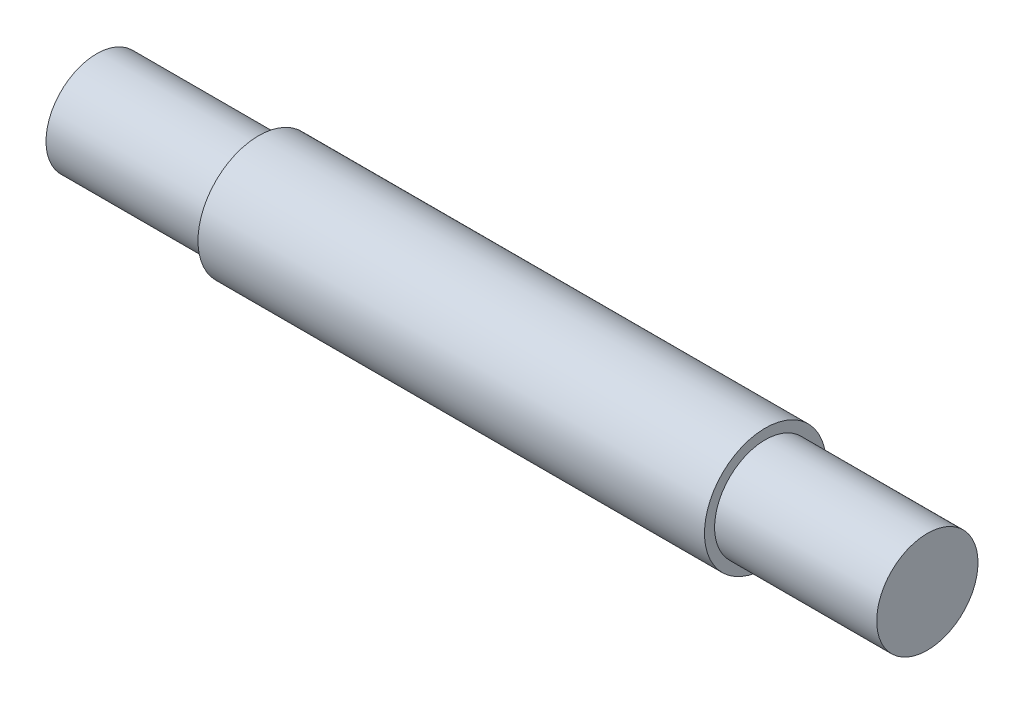
SolidWorks part; units mm, degrees
ref_plane "Ön Düzlem" through (0, 0, 0) normal (0, 0, 1) x (1, 0, 0)
ref_plane "Üst Düzlem" through (0, 0, 0) normal (0, 1, 0) x (1, 0, 0)
ref_plane "Sağ Düzlem" through (0, 0, 0) normal (1, 0, 0) x (0, 0, -1)
sketch "Çizim1" plane through (0, 0, 0) normal (1, 0, 0) x (0, 0, -1)
  circle A0 centre (0, 0) radius 6
extrude "Yükseklik-Ekstrüzyon1" add sketch "Çizim1" along normal blind 50
sketch "Çizim2" plane through (0, 0, 0) normal (-1, 0, 0) x (0, 0, 1)
  circle A0 centre (0, 0) radius 5
extrude "Yükseklik-Ekstrüzyon2" add sketch "Çizim2" along normal blind 16
sketch "Çizim3" plane through (50, 0, 0) normal (1, 0, 0) x (0, 0, -1)
  circle A0 centre (0, 0) radius 5
extrude "Yükseklik-Ekstrüzyon3" add sketch "Çizim3" along normal blind 16
